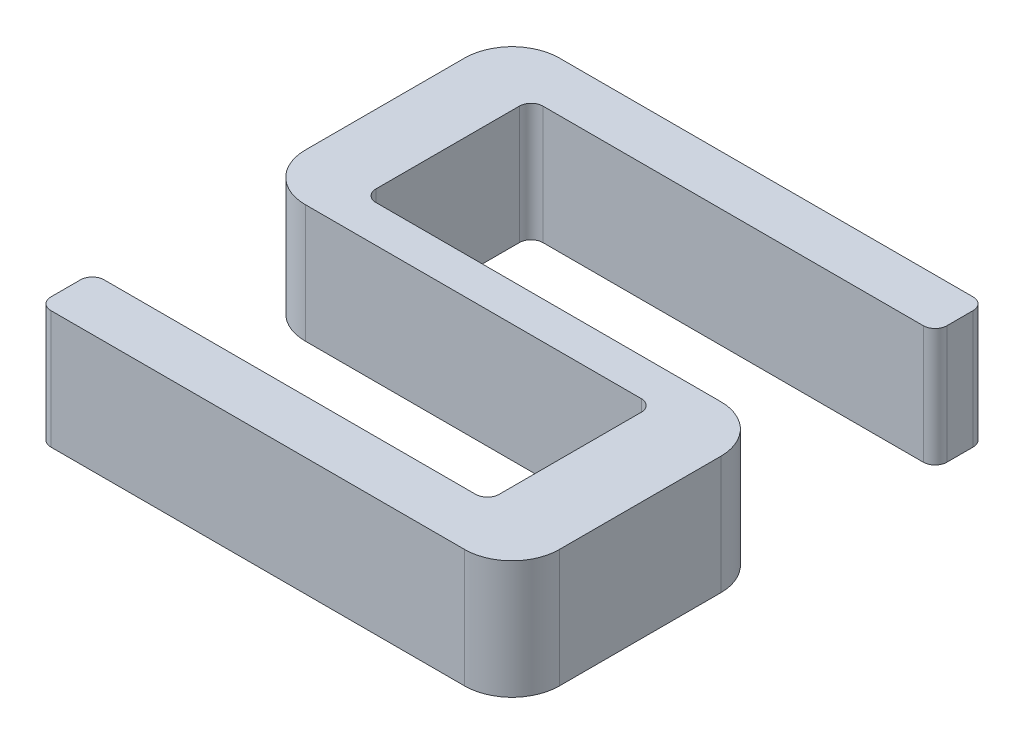
SolidWorks part; units mm, degrees
ref_plane "Front Plane" through (0, 0, 0) normal (0, 0, 1) x (1, 0, 0)
ref_plane "Top Plane" through (0, 0, 0) normal (0, 1, 0) x (1, 0, 0)
ref_plane "Right Plane" through (0, 0, 0) normal (1, 0, 0) x (0, 0, -1)
sketch "Sketch1" plane through (0, 0, 0) normal (0, 1, 0) x (1, 0, 0)
  line L1 (0, 0) -> (40, 0)
  line L2 (0, 0) -> (0, 4.5041)
  line L3 (0, 40) -> (40, 40)
  line L4 (40, 0) -> (40, 21.6577)
  line L5 (33.4153, 18.5185) -> (33.4153, 4.5041)
  line L6 (40, 40) -> (0, 40)
  line L7 (40, 40) -> (40, 35.7842)
  line L8 (40, 35.7842) -> (5.835, 35.7842)
  line L9 (0, 40) -> (0, 35.7842)
  line L18 (0, 40) -> (5.835, 40)
  line L19 (0, 40) -> (0, 21.6577)
  line L21 (5.835, 35.7842) -> (5.835, 21.6577)
  line L22 (5.835, 21.6577) -> (40, 21.6577)
  line L23 (0, 21.6577) -> (0, 18.5185)
  line L24 (0, 18.5185) -> (33.4153, 18.5185)
  line L25 (40, 21.6577) -> (40, 18.5185)
  line L26 (40, 21.6577) -> (33.4153, 21.6577)
  line L27 (40, 21.6577) -> (40, 0)
  line L28 (40, 0) -> (33.4153, 0)
  line L30 (40, 0) -> (0, 0)
  line L31 (40, 0) -> (40, 4.5041)
  line L32 (33.4153, 4.5041) -> (0, 4.5041)
  line L33 (0, 0) -> (0, 4.5041)
  line L35 (40, 35.7842) -> (40, 40)
  line L36 (0, 18.5185) -> (0, 40)
  point P5 (0, 0)
  dimension "D1" = 40
  dimension "D2" = 40
extrude "Boss-Extrude1" add sketch "Sketch1" along normal blind 10 contours L5 L32 L2 L1 L4 L27 L22 L21 L8 L7 L6 L3 L9 L19 L23 L24
fillet "Fillet1" radius 4 4 edges at (40, 5, 0) (40, 5, -21.6577) (0, 5, -18.5185) (0, 5, -40)
fillet "Fillet2" radius 1 8 edges at (0, 5, 0) (0, 5, -4.5041) (33.4153, 5, -4.5041) (33.4153, 5, -18.5185) (5.835, 5, -35.7842) (5.835, 5, -21.6577) (40, 5, -35.7842) (40, 5, -40)
